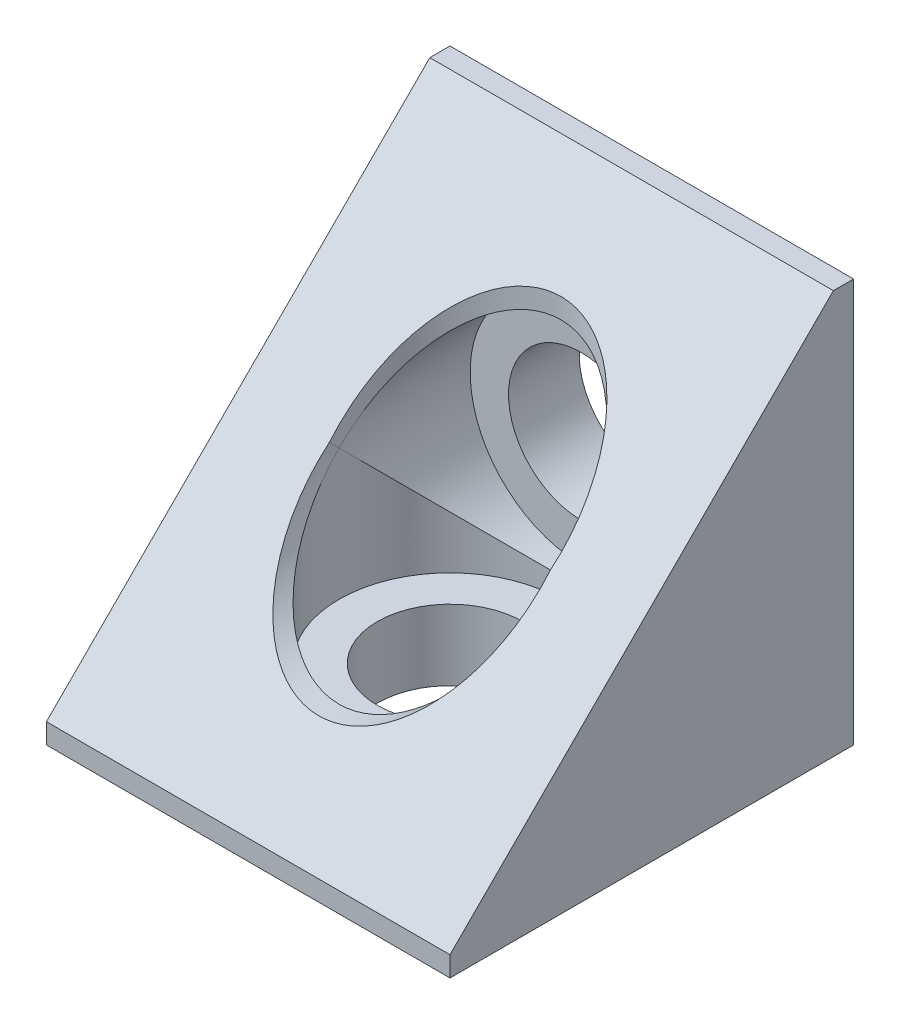
SolidWorks part; units mm, degrees
material "6061-T6 (SS)"
ref_plane "Front Plane" through (0, 0, 0) normal (0, 0, 1) x (1, 0, 0)
ref_plane "Top Plane" through (0, 0, 0) normal (0, 1, 0) x (1, 0, 0)
ref_plane "Right Plane" through (0, 0, 0) normal (1, 0, 0) x (0, 0, -1)
sketch "Sketch1" plane through (0, 0, 0) normal (0, 0, 1) x (1, 0, 0)
  line L1 (10, -10) -> (-10, -10)
  line L2 (10, -10) -> (10, 10)
  line L3 (10, 10) -> (-10, 10)
  line L4 (-10, -10) -> (-10, 10)
  line L5 (10, -10) -> (-10, 10) construction
  line L6 (10, 10) -> (-10, -10) construction
  circle A0 centre (0, 0) radius 3.6
  point P0 (0, 0)
  dimension "D2" = 7.2
  dimension "D1" = 20
extrude "Boss-Extrude1" add sketch "Sketch1" along normal mid plane 20
sketch "Sketch2" plane through (0, 0, 10) normal (0, 0, 1) x (1, 0, 0)
  circle A0 centre (0, 0) radius 5.5
  dimension "D1" = 11
extrude "Cut-Extrude1" cut sketch "Sketch2" against normal blind 16.5
sketch "Sketch4" plane through (0, 10, 0) normal (0, 1, 0) x (1, 0, 0)
  circle A0 centre (0, 0) radius 3.6
  dimension "D1" = 7.2
extrude "Cut-Extrude2" cut sketch "Sketch4" against normal through all
sketch "Sketch5" plane through (0, 10, 0) normal (0, 1, 0) x (1, 0, 0)
  circle A0 centre (0, 0) radius 5.5
  dimension "D1" = 11
extrude "Cut-Extrude3" cut sketch "Sketch5" against normal blind 16.5
sketch "Sketch6" plane through (10, 0, 0) normal (1, 0, 0) x (0, 0, -1)
  line L0 (-10, -9) -> (9, 10)
  line L1 (-10, -10) -> (-10, 10) construction
  line L2 (-10, 10) -> (10, 10) construction
  line L3 (9, 10) -> (-10, 10)
  line L4 (-10, 10) -> (-10, -9)
  line L5 (-10, -10) -> (10, -10) construction
  dimension "D1" = 1
  dimension "D2" = 45
extrude "Cut-Extrude4" cut sketch "Sketch6" against normal through all
